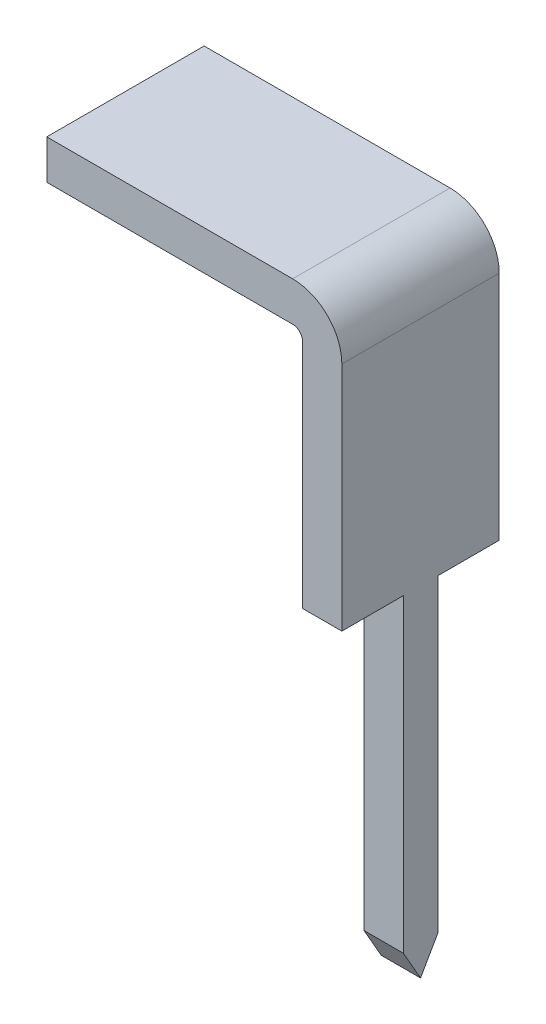
SolidWorks part; units mm, degrees
ref_plane "Front Plane" through (0, 0, 0) normal (0, 0, 1) x (1, 0, 0)
ref_plane "Top Plane" through (0, 0, 0) normal (0, 1, 0) x (1, 0, 0)
ref_plane "Right Plane" through (0, 0, 0) normal (1, 0, 0) x (0, 0, -1)
sketch "Sketch1" plane through (0, 0, 0) normal (0, 0, 1) x (1, 0, 0)
  line L0 (0, 0) -> (0, 5.5)
  line L1 (-0.5, 6) -> (-3, 6)
  line L2 (-0.4, 0) -> (-0.4, 5.5)
  line L3 (-0.5, 5.6) -> (-3, 5.6)
  line L4 (-3, 6) -> (-3, 5.6)
  line L5 (-0.4, 0) -> (0, 0)
  arc A0 (0, 5.5) -> (-0.5, 6) centre (-0.5, 5.5) ccw
  arc A1 (-0.4, 5.5) -> (-0.5, 5.6) centre (-0.5, 5.5) ccw
  point P6 (0, 6)
  dimension "D3" = 0.5
  dimension "D1" = 6
  dimension "D2" = 3
  dimension "D4" = 0.4
extrude "Boss-Extrude1" add sketch "Sketch1" along normal blind 1.6
sketch "Sketch2" plane through (0, 0, 0) normal (1, 0, 0) x (0, 0, -1)
  line L0 (-1.6, 0) -> (-1.6, 5.5) construction
  line L1 (-1.6, 3.1481) -> (-0.975, 3.1481)
  line L2 (-1.6, 3.1481) -> (-1.6, -0.3519)
  line L3 (-1.6, -0.3519) -> (-0.975, -0.3519)
  line L4 (-0.975, 3.1481) -> (-0.975, -0.3519)
  line L5 (-0.8, 0) -> (-0.8, 6.4853) construction
  line L6 (-1.6, 0) -> (0, 0) construction
  line L7 (0, -0.3519) -> (-0.625, -0.3519)
  line L8 (0, 3.1481) -> (0, -0.3519)
  line L9 (0, 3.1481) -> (-0.625, 3.1481)
  line L10 (-0.625, 3.1481) -> (-0.625, -0.3519)
  dimension "D1" = 0.35
  dimension "D2" = 3.5
extrude "Cut-Extrude1" cut sketch "Sketch2" against normal blind 1.6
sketch "Sketch3" plane through (0, 0, 0) normal (1, 0, 0) x (0, 0, -1)
  line L0 (-0.975, 0) -> (-0.8, -0.3056)
  line L1 (-0.8, -0.3056) -> (-0.625, 0)
  line L10 (-0.975, 0) -> (-0.625, 0)
  line L11 (-0.625, 0) -> (-0.625, 3.1481)
  line L12 (-0.625, 3.1481) -> (0, 3.1481)
  line L13 (0, 3.1481) -> (0, 5.5)
  line L14 (0, 5.5) -> (-1.6, 5.5)
  line L15 (-1.6, 5.5) -> (-1.6, 3.1481)
  line L16 (-1.6, 3.1481) -> (-0.975, 3.1481)
  line L17 (-0.975, 3.1481) -> (-0.975, 0)
  line L18 (-0.975, 0) -> (-0.625, 0)
  dimension "D1" = 0.175
  dimension "D2" = 0
extrude "Boss-Extrude2" add sketch "Sketch3" against normal up to surface (0.4 mm away) up to face at (-0.4, 2.9491, 0.8)
